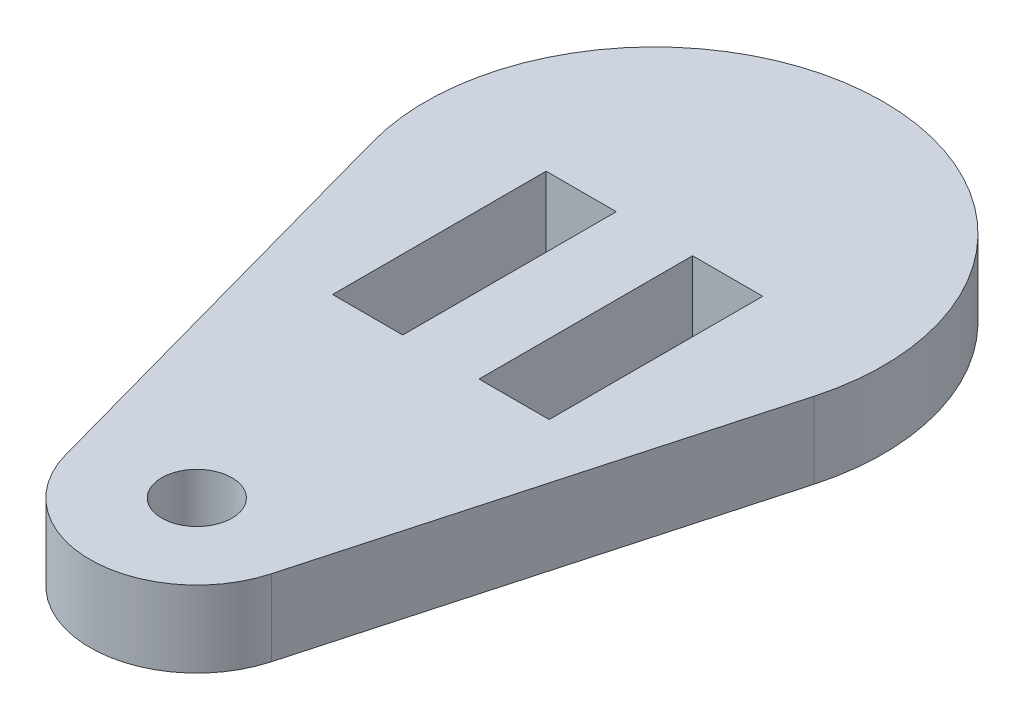
SolidWorks part; units mm, degrees
ref_plane "Front Plane" through (0, 0, 0) normal (0, 0, 1) x (1, 0, 0)
ref_plane "Top Plane" through (0, 0, 0) normal (0, 1, 0) x (1, 0, 0)
ref_plane "Right Plane" through (0, 0, 0) normal (1, 0, 0) x (0, 0, -1)
sketch "Sketch1" plane through (0, 0, 0) normal (0, 1, 0) x (1, 0, 0)
  line L0 (0, 0) -> (0, -42.8356) construction
  line L1 (-9.1801, -2.54) -> (-4.284, -20.2353)
  line L2 (9.1801, -2.54) -> (4.284, -20.2353)
  circle A0 centre (0, 0) radius 9.525
  circle A1 centre (0, -19.05) radius 4.445
  circle A3 centre (0, -19.05) radius 1.4605
  dimension "D1" = 19.05
  dimension "D2" = 8.89
  dimension "D4" = 2.921
  dimension "D3" = 19.05
extrude "Boss-Extrude1" add sketch "Sketch1" along normal mid plane 3.175
sketch "Sketch2" plane through (0, 1.5875, 0) normal (0, 1, 0) x (1, 0, 0)
  line L0 (0, 0) -> (0, -27.4063) construction
  line L2 (-1.5875, 0) -> (-4.5085, 0)
  line L3 (-1.5875, 0) -> (-1.5875, -8.89)
  line L4 (-1.5875, -8.89) -> (-4.5085, -8.89)
  line L5 (-4.5085, 0) -> (-4.5085, -8.89)
  line L6 (-1.5875, 0) -> (-4.5085, -8.89) construction
  line L7 (-1.5875, -8.89) -> (-4.5085, 0) construction
  point P3 (-3.048, -4.445)
  dimension "D1" = 2.921
  dimension "D2" = 8.89
  dimension "D3" = 1.5875
extrude "Cut-Extrude1" cut sketch "Sketch2" against normal through all both and the other way through all
mirror "Mirror1" about plane through (0, 0, 0) normal (1, 0, 0) of "Cut-Extrude1"
